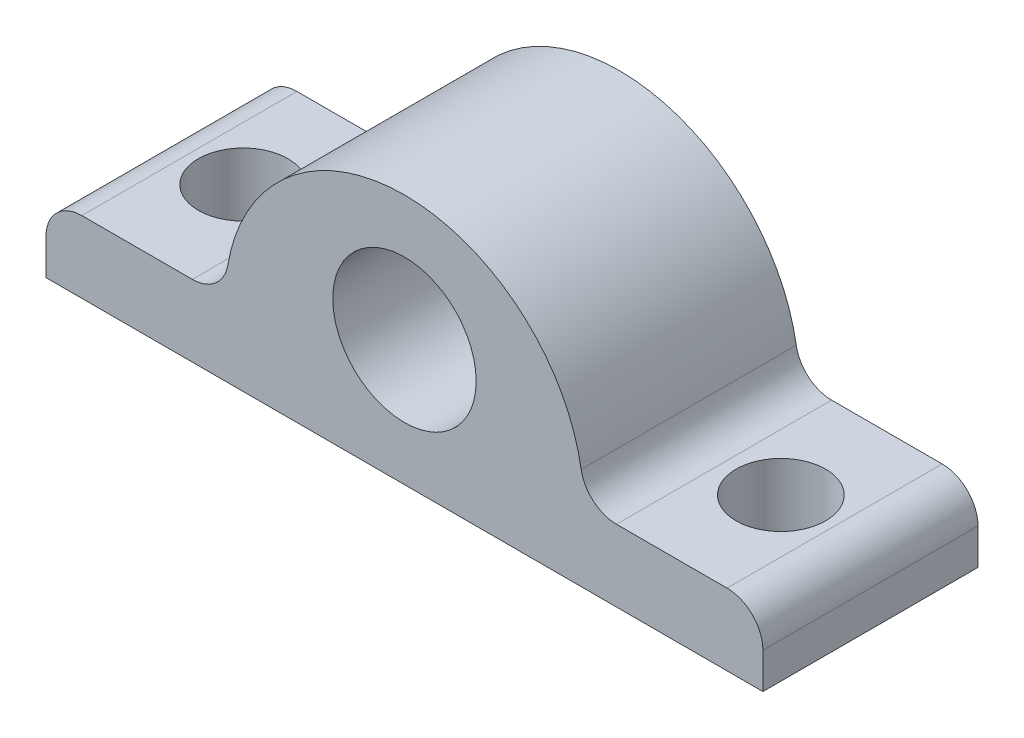
SolidWorks part; units mm, degrees
ref_plane "Front Plane" through (0, 0, 0) normal (0, 0, 1) x (1, 0, 0)
ref_plane "Top Plane" through (0, 0, 0) normal (0, 1, 0) x (1, 0, 0)
ref_plane "Right Plane" through (0, 0, 0) normal (1, 0, 0) x (0, 0, -1)
sketch "Sketch1" plane through (0, 0, 0) normal (0, 1, 0) x (1, 0, 0)
  line L1 (-20, 6) -> (20, 6)
  line L2 (-20, 6) -> (-20, -6)
  line L3 (-20, -6) -> (20, -6)
  line L4 (20, 6) -> (20, -6)
  line L5 (-20, 6) -> (20, -6) construction
  line L6 (-20, -6) -> (20, 6) construction
  point P0 (0, 0)
  dimension "D1" = 40
  dimension "D2" = 12
extrude "Boss-Extrude1" add sketch "Sketch1" along normal blind 4
sketch "Sketch2" plane through (0, 0, 6) normal (0, 0, 1) x (1, 0, 0)
  line L0 (0, 0) -> (0, 13.1444) construction
  line L1 (-20, 0) -> (20, 0) construction
  line L2 (-20, 4) -> (20, 4) construction
  line L3 (20, 4) -> (10, 4)
  line L7 (-20, 0) -> (20, 0)
  line L8 (20, 0) -> (20, 4)
  line L9 (20, 4) -> (-20, 4)
  line L10 (-20, 4) -> (-20, 0)
  line L11 (-20, 0) -> (20, 0)
  line L12 (20, 0) -> (20, 4)
  line L13 (-10, 4) -> (-20, 4)
  line L14 (-20, 4) -> (-20, 0)
  arc A0 (-10, 4) -> (10, 4) centre (0, 4) cw
  point P6 (0, 0)
  point P9 (0, 0)
  point P10 (0, 0)
  dimension "D1" = 10
  dimension "D2" = 0
extrude "Boss-Extrude2" add sketch "Sketch2" against normal up to surface (12 mm away) up to face at (0, 2, -6)
sketch "Sketch3" plane through (0, 0, 6) normal (0, 0, 1) x (1, 0, 0)
  circle A0 centre (0, 7) radius 4
  point P2 (0, 0)
  dimension "D1" = 8
  dimension "D2" = 7
extrude "Cut-Extrude1" cut sketch "Sketch3" against normal through all
sketch "Sketch4" plane through (0, 4, 0) normal (0, 1, 0) x (1, 0, 0)
  circle A0 centre (-15, 0) radius 2.5
  circle A1 centre (15, 0) radius 2.5
  point P4 (0, 0)
  dimension "D1" = 5
  dimension "D2" = 15
  dimension "D3" = 15
extrude "Cut-Extrude2" cut sketch "Sketch4" against normal through all
fillet "Fillet1" radius 2 4 edges at (-10, 4, 0) (10, 4, 0) (20, 4, 0) (-20, 4, 0)
